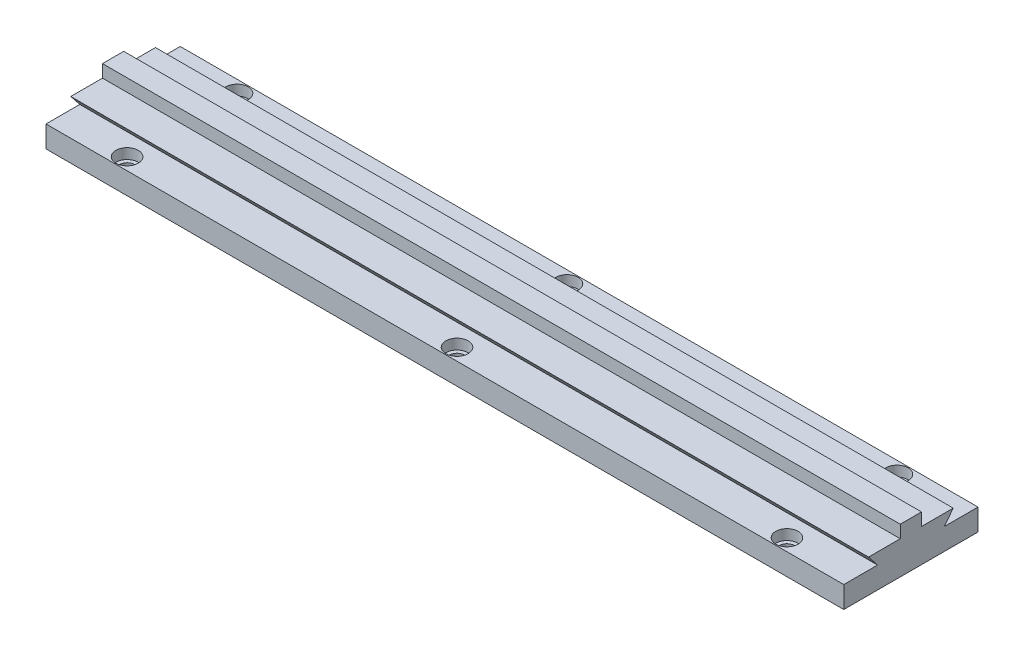
SolidWorks part; units mm, degrees
ref_plane "Front Plane" through (0, 0, 0) normal (0, 0, 1) x (1, 0, 0)
ref_plane "Top Plane" through (0, 0, 0) normal (0, 1, 0) x (1, 0, 0)
ref_plane "Right Plane" through (0, 0, 0) normal (1, 0, 0) x (0, 0, -1)
sketch "Sketch1" plane through (0, 0, 0) normal (1, 0, 0) x (0, 0, -1)
  line L0 (-31, 0) -> (31, 0)
  line L1 (0, 16.048) -> (0, -17.4571) construction
  line L2 (-31, 0) -> (-31, 10)
  line L3 (-31, 10) -> (-15.4, 10)
  line L4 (-15.4, 10) -> (-19.57, 15.28)
  line L5 (-19.57, 15.28) -> (-4.91, 15.28)
  line L6 (15.4, 10) -> (19.57, 15.28)
  line L7 (31, 10) -> (15.4, 10)
  line L8 (31, 0) -> (31, 10)
  line L9 (-4.91, 15.28) -> (-4.91, 21.1)
  line L10 (-4.91, 21.1) -> (4.91, 21.1)
  line L11 (4.91, 15.28) -> (4.91, 21.1)
  line L12 (4.91, 15.28) -> (19.57, 15.28)
  point P6 (0, 0)
  point P11 (0, 21.1)
  point P17 (0, 21.1)
  dimension "D1" = 62
  dimension "D2" = 10
  dimension "D3" = 21.1
  dimension "D4" = 9.82
  dimension "D5" = 5.82
  dimension "D6" = 15.4
  dimension "D7" = 19.57
extrude "Boss-Extrude1" add sketch "Sketch1" along normal blind 368.5
hole_wizard "CBORE for 1/4 Socket Shoulder Screw1" positions "Sketch3" profile "Sketch4" counterbore size "1/4" standard "ANSI Inch" end condition through all
sketch "Sketch3" plane through (0, 10, 0) normal (0, 1, 0) x (1, 0, 0)
  line L1 (31.85, 25.4) -> (184.25, 25.4) construction
  line L3 (-8.755, 0) -> (155.4594, 0) construction
  line L5 (31.85, -25.4) -> (184.25, -25.4) construction
  line L7 (184.25, 25.4) -> (184.25, -25.4) construction
  line L9 (184.25, 25.4) -> (336.65, 25.4) construction
  line L12 (184.25, -25.4) -> (336.65, -25.4) construction
  line L13 (336.65, -25.4) -> (336.65, 25.4) construction
  line L15 (368.5, 31) -> (368.5, 15.4) construction
  point P0 (31.85, 25.4)
  point P2 (184.25, 25.4)
  point P4 (336.65, 25.4)
  point P6 (336.65, -25.4)
  point P8 (184.25, -25.4)
  point P10 (31.85, -25.4)
  dimension "D1" = 50.8
  dimension "D2" = 25.4
  dimension "D3" = 152.4
  dimension "D4" = 152.4
  dimension "D5" = 31.85
sketch "Sketch4" plane through (31.85, 10, -25.4) normal (1, 0, 0) x (0, 0, 1)
  line L0 (0, 0) -> (0, 10)
  line L1 (0, 10) -> (3.3782, 10)
  line L3 (3.3782, 10) -> (3.3782, 4.7752)
  line L4 (3.3782, 4.7752) -> (5.1587, 4.7752)
  line L5 (5.1587, 4.7752) -> (5.1587, 0)
  line L7 (5.1587, 0) -> (0, 0)
  line L11 (0, -6.35) -> (0, 107.95) construction
  dimension "Thru Hole Dia." = 6.7564
  dimension "Thru Hole Depth" = 10
  dimension "C'Bore Dia." = 10.3175
  dimension "C'Bore Depth" = 4.7752
